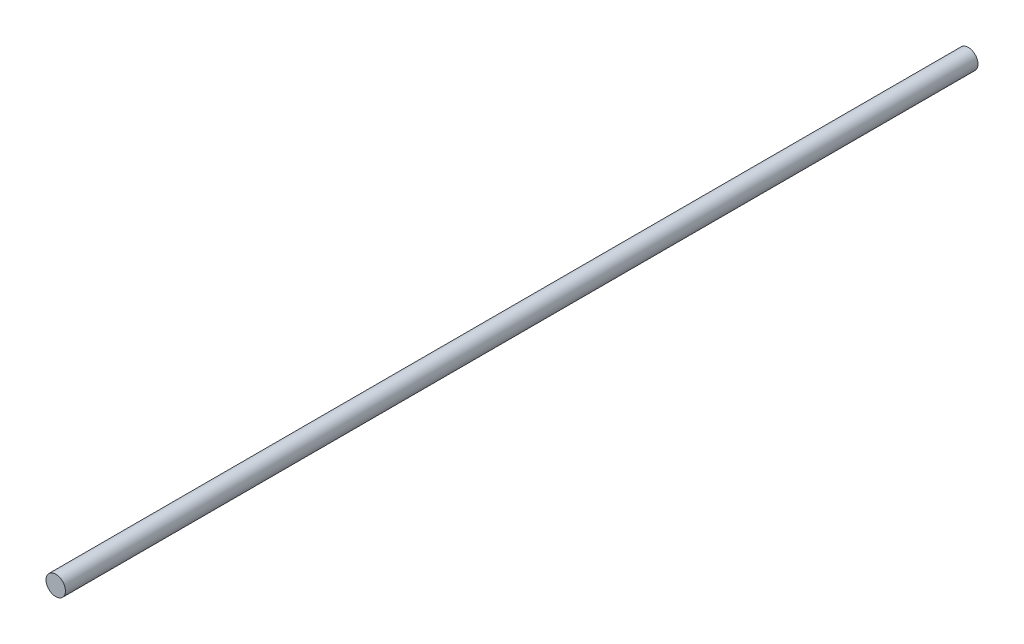
SolidWorks part; units mm, degrees
ref_plane "Front Plane" through (0, 0, 0) normal (0, 0, 1) x (1, 0, 0)
ref_plane "Top Plane" through (0, 0, 0) normal (0, 1, 0) x (1, 0, 0)
ref_plane "Right Plane" through (0, 0, 0) normal (1, 0, 0) x (0, 0, -1)
sketch "Esboço1" plane through (0, 0, 0) normal (0, 0, 1) x (1, 0, 0)
  circle A0 centre (-48.8753, 81.4072) radius 4
  dimension "D1" = 8
extrude "Ressalto-extrusão1" add sketch "Esboço1" along normal blind 375 contours A0
